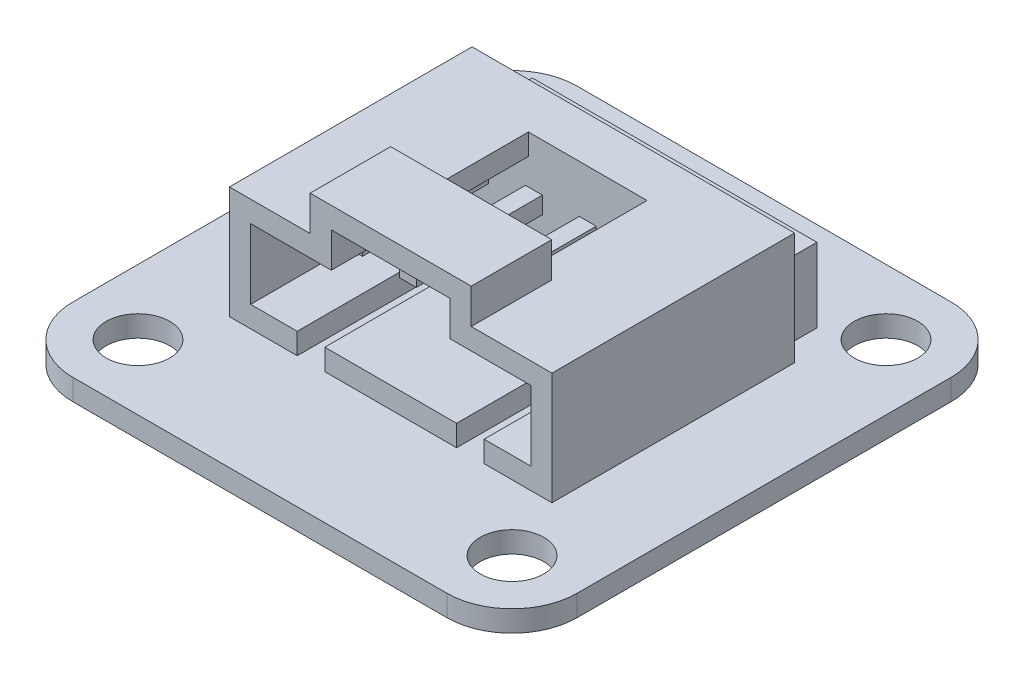
SolidWorks part; units mm, degrees
ref_plane "Front Plane" through (0, 0, 0) normal (0, 0, 1) x (1, 0, 0)
ref_plane "Top Plane" through (0, 0, 0) normal (0, 1, 0) x (1, 0, 0)
ref_plane "Right Plane" through (0, 0, 0) normal (1, 0, 0) x (0, 0, -1)
sketch "Sketch1" plane through (0, 0, 0) normal (0, 1, 0) x (1, 0, 0)
  line L0 (0, 11.9) -> (0, -11.9) construction
  line L1 (-11.9, 11.9) -> (11.9, 11.9)
  line L2 (-11.9, 11.9) -> (-11.9, -11.9)
  line L3 (-11.9, -11.9) -> (11.9, -11.9)
  line L4 (11.9, 11.9) -> (11.9, -11.9)
  line L5 (-11.9, 11.9) -> (11.9, -11.9) construction
  line L6 (-11.9, -11.9) -> (11.9, 11.9) construction
  line L7 (-11.9, 0) -> (11.9, 0) construction
  line L9 (8.825, -8.825) -> (-8.825, -8.825)
  line L10 (8.825, -8.825) -> (8.825, 8.825)
  line L11 (8.825, 8.825) -> (-8.825, 8.825)
  line L12 (-8.825, -8.825) -> (-8.825, 8.825)
  line L13 (8.825, -8.825) -> (-8.825, 8.825) construction
  line L14 (8.825, 8.825) -> (-8.825, -8.825) construction
  circle A0 centre (-8.825, 8.825) radius 1.5
  circle A1 centre (8.825, 8.825) radius 1.5
  circle A2 centre (8.825, -8.825) radius 1.5
  circle A3 centre (-8.825, -8.825) radius 1.5
  circle A4 centre (-8.825, 8.825) radius 3.075
  circle A5 centre (8.825, 8.825) radius 3.075
  circle A6 centre (-8.825, -8.825) radius 3.075
  circle A7 centre (8.825, -8.825) radius 3.075
  point P0 (0, 0)
  point P12 (0, 0)
  dimension "D3" = 3
  dimension "D1" = 23.8
  dimension "D2" = 17.65
extrude "Boss-Extrude1" add sketch "Sketch1" along normal blind 1 contours L11 A5 L1 A4 | L11 A4 L12 A0 | L12 A4 L11 A0 | A7 L10 A5 L11 A4 L12 A6 L9 | A5 L11 A1 L10 | A5 L10 A1 L11 | A7 L4 A5 L10 | A7 L10 A2 L9 | L10 A7 L9 A2 | A7 L9 A6 L3 | A6 L12 A3 L9 | L2 A6 L12 A4 | A6 L9 A3 L12
sketch "Sketch2" plane through (0, 1, 0) normal (0, 1, 0) x (1, 0, 0)
  line L1 (-7.61, 5.725) -> (7.61, 5.725)
  line L2 (-7.61, 5.725) -> (-7.61, -5.725)
  line L3 (-7.61, -5.725) -> (7.61, -5.725)
  line L4 (7.61, 5.725) -> (7.61, -5.725)
  line L5 (-7.61, 5.725) -> (7.61, -5.725) construction
  line L6 (-7.61, -5.725) -> (7.61, 5.725) construction
  point P0 (0, 0)
  dimension "D1" = 15.22
  dimension "D2" = 11.45
extrude "Boss-Extrude2" add sketch "Sketch2" along normal blind 5.3
sketch "Sketch3" plane through (0, 1, 0) normal (0, 1, 0) x (1, 0, 0)
  line L0 (0, 11.9) -> (0, -11.9) construction
  line L1 (-8.825, 11.9) -> (8.825, 11.9) construction
  line L2 (-8.825, -11.9) -> (8.825, -11.9) construction
  line L3 (7.61, 5.725) -> (-7.61, 5.725) construction
  line L4 (-6.715, 7.675) -> (6.715, 7.675)
  line L5 (-6.715, 7.675) -> (-6.715, 5.725)
  line L6 (-6.715, 5.725) -> (6.715, 5.725)
  line L7 (6.715, 7.675) -> (6.715, 5.725)
  line L8 (-6.715, 7.675) -> (6.715, 5.725) construction
  line L9 (-6.715, 5.725) -> (6.715, 7.675) construction
  point P6 (0, 6.7)
  dimension "D1" = 13.43
  dimension "D2" = 1.95
extrude "Boss-Extrude3" add sketch "Sketch3" along normal blind 3.5
sketch "Sketch5" plane through (0, 6.3, 0) normal (0, 1, 0) x (1, 0, 0)
  line L0 (0, 5.725) -> (0, -5.725) construction
  line L1 (7.61, 5.725) -> (-7.61, 5.725) construction
  line L2 (-7.61, -5.725) -> (7.61, -5.725) construction
  line L3 (-7.61, -5.725) -> (7.61, -5.725) construction
  line L4 (-3.8, -1.925) -> (3.8, -1.925)
  line L5 (-3.8, -1.925) -> (-3.8, -5.725)
  line L6 (-3.8, -5.725) -> (3.8, -5.725)
  line L7 (3.8, -1.925) -> (3.8, -5.725)
  line L8 (-3.8, -1.925) -> (3.8, -5.725) construction
  line L9 (-3.8, -5.725) -> (3.8, -1.925) construction
  point P6 (0, -3.825)
  dimension "D1" = 7.6
  dimension "D2" = 3.8
extrude "Boss-Extrude4" add sketch "Sketch5" along normal blind 1.65
sketch "Sketch4" plane through (0, 0, 5.725) normal (0, 0, 1) x (1, 0, 0)
  line L0 (-7.61, 6.3) -> (7.61, 1) construction
  line L1 (-6.61, 5.3) -> (-7.61, 5.3) construction
  line L2 (6.61, 5.3) -> (-6.61, 5.3)
  line L3 (6.61, 5.3) -> (6.61, 2)
  line L4 (6.61, 2) -> (-6.61, 2)
  line L5 (-6.61, 5.3) -> (-6.61, 2)
  line L6 (6.61, 5.3) -> (-6.61, 2) construction
  line L7 (6.61, 2) -> (-6.61, 5.3) construction
  line L8 (-7.61, 6.3) -> (-7.61, 1) construction
  line L9 (-6.61, 5.3) -> (-6.61, 6.3) construction
  line L10 (-7.61, 6.3) -> (-3.8, 6.3) construction
  line L11 (0, 7.95) -> (0, 0) construction
  line L12 (-3.8, 7.95) -> (3.8, 7.95) construction
  line L13 (-2.8, 6.95) -> (-3.8, 6.95) construction
  line L14 (-2.8, 6.95) -> (2.8, 6.95)
  line L15 (-2.8, 6.95) -> (-2.8, 5.3)
  line L16 (-2.8, 5.3) -> (2.8, 5.3)
  line L17 (2.8, 6.95) -> (2.8, 5.3)
  line L18 (-2.8, 6.95) -> (2.8, 5.3) construction
  line L19 (-2.8, 5.3) -> (2.8, 6.95) construction
  line L20 (-3.8, 7.95) -> (-3.8, 6.3) construction
  line L21 (-2.8, 6.95) -> (-2.8, 7.95) construction
  line L22 (-7.61, 1) -> (7.61, 1) construction
  line L23 (-4.41, 2) -> (-3.11, 2)
  line L24 (-4.41, 2) -> (-4.41, 1)
  line L25 (-4.41, 1) -> (-3.11, 1)
  line L26 (-3.11, 2) -> (-3.11, 1)
  line L27 (4.41, 2) -> (3.11, 2)
  line L28 (4.41, 2) -> (4.41, 1)
  line L29 (4.41, 1) -> (3.11, 1)
  line L30 (3.11, 2) -> (3.11, 1)
  point P4 (0, 3.65)
  point P20 (0, 6.125)
  line M4 (-7.61, 1) -> (7.61, 1)
  dimension "D1" = 1
  dimension "D2" = 3.2
  dimension "D3" = 1.3
extrude "Cut-Extrude1" cut sketch "Sketch4" against normal blind 9.3 contours L2 L5 L4 L3 | L17 L14 L15 L2 | L26 L4 L24 M4 | L4 L30 L28 M4
sketch "Sketch6" plane through (0, 0, -3.575) normal (0, 0, 1) x (1, 0, 0)
  line L0 (-6.61, 3.65) -> (6.61, 3.65) construction
  line L1 (-6.61, 5.3) -> (-6.61, 2) construction
  line L2 (6.61, 5.3) -> (6.61, 2) construction
  line L3 (2.14, 3.25) -> (2.94, 3.25)
  line L4 (-0.4, 4.05) -> (0.4, 4.05)
  line L5 (-0.4, 4.05) -> (-0.4, 3.25)
  line L6 (-0.4, 3.25) -> (0.4, 3.25)
  line L7 (0.4, 4.05) -> (0.4, 3.25)
  line L8 (-0.4, 4.05) -> (0.4, 3.25) construction
  line L9 (-0.4, 3.25) -> (0.4, 4.05) construction
  line L10 (2.94, 4.05) -> (2.94, 3.25)
  line L11 (2.14, 4.05) -> (2.94, 4.05)
  line L12 (2.14, 4.05) -> (2.14, 3.25)
  line L13 (4.68, 3.25) -> (5.48, 3.25)
  line L14 (5.48, 4.05) -> (5.48, 3.25)
  line L15 (4.68, 4.05) -> (5.48, 4.05)
  line L16 (4.68, 4.05) -> (4.68, 3.25)
  line L17 (-2.94, 3.25) -> (-2.14, 3.25)
  line L18 (-2.14, 4.05) -> (-2.14, 3.25)
  line L19 (-2.94, 4.05) -> (-2.14, 4.05)
  line L20 (-2.94, 4.05) -> (-2.94, 3.25)
  line L21 (-5.48, 3.25) -> (-4.68, 3.25)
  line L22 (-4.68, 4.05) -> (-4.68, 3.25)
  line L23 (-5.48, 4.05) -> (-4.68, 4.05)
  line L24 (-5.48, 4.05) -> (-5.48, 3.25)
  point P6 (0, 3.65)
  dimension "D1" = 0.8
  dimension "D3" = 2.54
  dimension "D5" = 2.54
  dimension "D2" = 3
  dimension "D4" = 3
extrude "Boss-Extrude5" add sketch "Sketch6" along normal offset from surface (5.95 mm away) 3.35 up to face at (0, 4.41, 5.725)
sketch "Sketch7" plane through (0, 0, 0) normal (0, -1, 0) x (1, 0, 0)
  line L1 (-2, 2.55) -> (2, 2.55)
  line L2 (-2, 2.55) -> (-2, -2.55)
  line L3 (-2, -2.55) -> (2, -2.55)
  line L4 (2, 2.55) -> (2, -2.55)
  line L5 (-2, 2.55) -> (2, -2.55) construction
  line L6 (-2, -2.55) -> (2, 2.55) construction
  point P0 (0, 0)
  dimension "D1" = 4
  dimension "D2" = 5.1
extrude "Boss-Extrude6" add sketch "Sketch7" along normal blind 1.6
fillet "Fillet1" radius 0.25 4 edges at (0, -1.6, -2.55) (-2, -1.6, 0) (0, -1.6, 2.55) (2, -1.6, 0)
